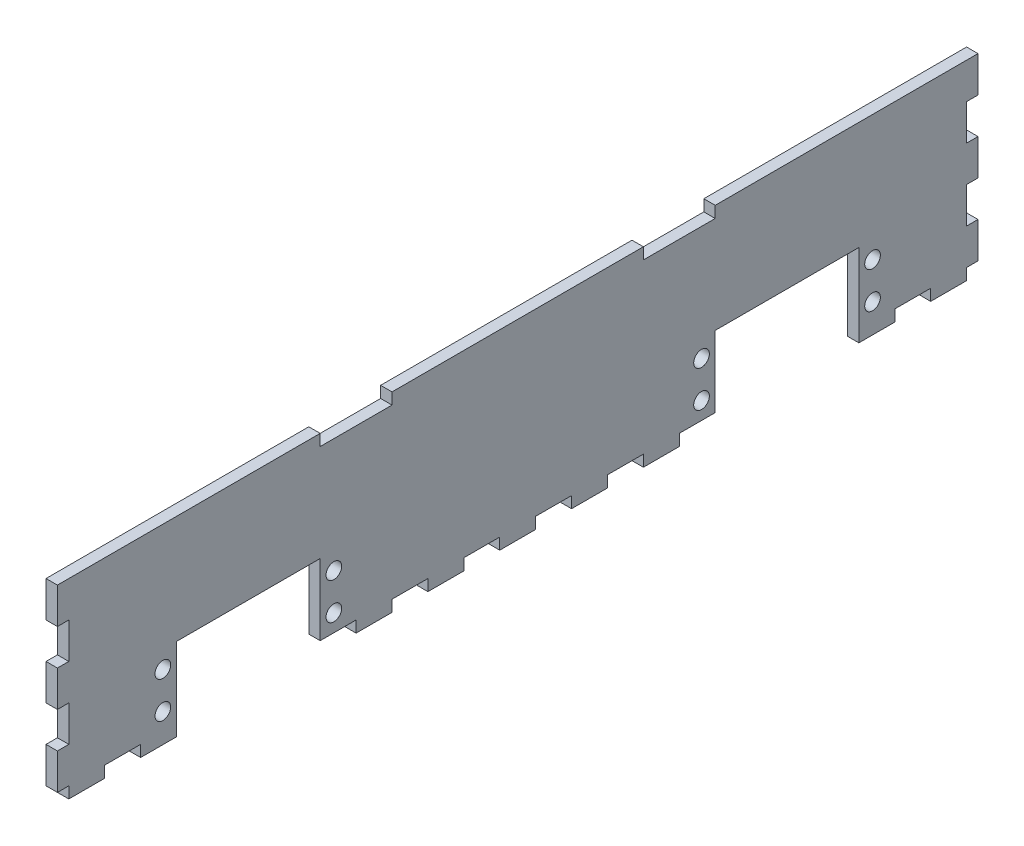
SolidWorks part; units mm, degrees
ref_plane "Plan de face" through (0, 0, 0) normal (0, 0, 1) x (1, 0, 0)
ref_plane "Plan de dessus" through (0, 0, 0) normal (0, 1, 0) x (1, 0, 0)
ref_plane "Plan de droite" through (0, 0, 0) normal (1, 0, 0) x (0, 0, -1)
sketch "Esquisse1" plane through (0, 0, 0) normal (1, 0, 0) x (0, 0, -1)
  line L1 (0, 0) -> (250, 0)
  line L2 (0, 0) -> (0, 50)
  line L3 (0, 50) -> (250, 50)
  line L4 (250, 0) -> (250, 50)
  dimension "D1" = 250
  dimension "D2" = 50
extrude "Boss.-Extru.1" add sketch "Esquisse1" along normal blind 3.175
sketch "Esquisse2" plane through (3.175, 0, 0) normal (1, 0, 0) x (0, 0, -1)
  line L1 (0, 0) -> (10, 0)
  line L2 (0, 0) -> (0, -3.175)
  line L3 (0, -3.175) -> (10, -3.175)
  line L4 (10, 0) -> (10, -3.175)
  dimension "D1" = 10
  dimension "D2" = 3.175
extrude "Boss.-Extru.2" add sketch "Esquisse2" against normal blind 3.175
pattern_linear "Répétition linéaire1" count 13 spacing 20 along (0, 0, -1) of "Boss.-Extru.2"
sketch "Esquisse4" plane through (3.175, 0, 0) normal (1, 0, 0) x (0, 0, -1)
  line L0 (250, 50) -> (0, 50) construction
  line L1 (30, -3.175) -> (70, -3.175)
  line L2 (30, -3.175) -> (30, 19.825)
  line L3 (30, 19.825) -> (70, 19.825)
  line L4 (70, -3.175) -> (70, 19.825)
  line L5 (220, -3.175) -> (180, -3.175)
  line L6 (220, -3.175) -> (220, 19.825)
  line L7 (220, 19.825) -> (180, 19.825)
  line L8 (180, -3.175) -> (180, 19.825)
  line L9 (70, 50) -> (90, 50)
  line L10 (70, 50) -> (70, 46.825)
  line L11 (70, 46.825) -> (90, 46.825)
  line L12 (90, 50) -> (90, 46.825)
  line L14 (180, 50) -> (160, 50)
  line L15 (180, 50) -> (180, 46.825)
  line L16 (180, 46.825) -> (160, 46.825)
  line L17 (160, 50) -> (160, 46.825)
  dimension "D1" = 23
  dimension "D2" = 23
  dimension "D3" = 3.175
  dimension "D4" = 3.175
extrude "Enlèv. mat.-Extru.1" cut sketch "Esquisse4" against normal blind 3.175
sketch "Esquisse5" plane through (3.175, 0, 0) normal (1, 0, 0) x (0, 0, -1)
  line L1 (0, 50) -> (-3.175, 50)
  line L2 (0, 50) -> (0, 40)
  line L3 (0, 40) -> (-3.175, 40)
  line L4 (-3.175, 50) -> (-3.175, 40)
  line L5 (250, 50) -> (253.175, 50)
  line L6 (250, 50) -> (250, 40)
  line L7 (250, 40) -> (253.175, 40)
  line L8 (253.175, 50) -> (253.175, 40)
  dimension "D1" = 3.175
  dimension "D2" = 10
  dimension "D3" = 10
  dimension "D4" = 3.175
extrude "Boss.-Extru.3" add sketch "Esquisse5" against normal blind 3.175
pattern_linear "Répétition linéaire2" count 3 spacing 20 along (0, -1, 0) of "Boss.-Extru.3"
sketch "Esquisse6" plane through (3.175, 0, 0) normal (1, 0, 0) x (0, 0, -1)
  line L0 (10, 0) -> (20, 0) construction
  line L1 (70, 0) -> (80, 0) construction
  line L2 (30, -3.175) -> (30, 19.825) construction
  line L3 (70, 0) -> (70, 19.825) construction
  line L4 (180, 19.825) -> (180, 0) construction
  line L5 (220, 19.825) -> (220, -3.175) construction
  line L6 (170, 0) -> (180, 0) construction
  line L8 (230, 0) -> (240, 0) construction
  circle A0 centre (73.81, 14.99) radius 2.18
  circle A1 centre (73.81, 4.83) radius 2.18
  circle A2 centre (26.19, 14.99) radius 2.18
  circle A3 centre (26.19, 4.83) radius 2.18
  circle A4 centre (176.19, 14.99) radius 2.18
  circle A5 centre (176.19, 4.83) radius 2.18
  circle A6 centre (223.81, 4.83) radius 2.18
  circle A7 centre (223.81, 14.99) radius 2.18
  dimension "D1" = 4.36
  dimension "D2" = 4.36
  dimension "D3" = 4.36
  dimension "D4" = 4.36
  dimension "D5" = 4.83
  dimension "D6" = 10.16
  dimension "D7" = 4.83
  dimension "D8" = 10.16
  dimension "D9" = 3.81
  dimension "D10" = 3.81
  dimension "D11" = 3.81
  dimension "D12" = 3.81
  dimension "D13" = 4.36
  dimension "D14" = 4.36
  dimension "D15" = 4.36
  dimension "D16" = 4.36
  dimension "D17" = 3.81
  dimension "D18" = 3.81
  dimension "D19" = 3.81
  dimension "D20" = 3.81
  dimension "D21" = 4.83
  dimension "D22" = 10.16
  dimension "D23" = 4.83
  dimension "D24" = 10.16
extrude "Enlèv. mat.-Extru.2" cut sketch "Esquisse6" against normal blind 10
